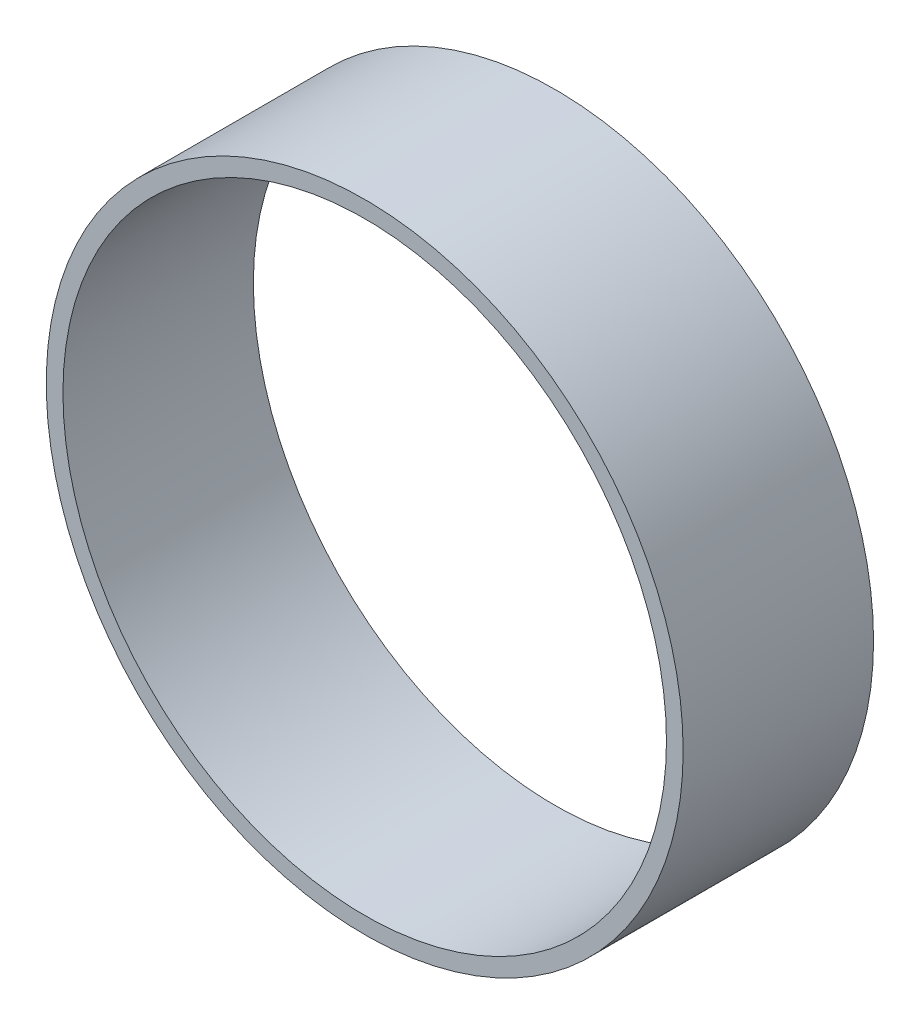
SolidWorks part; units mm, degrees
ref_plane "Front Plane" through (0, 0, 0) normal (0, 0, 1) x (1, 0, 0)
ref_plane "Top Plane" through (0, 0, 0) normal (0, 1, 0) x (1, 0, 0)
ref_plane "Right Plane" through (0, 0, 0) normal (1, 0, 0) x (0, 0, -1)
sketch "Sketch2" plane through (0, 0, 0) normal (0, 1, 0) x (1, 0, 0)
  line L0 (0, 0) -> (-48.5, 0)
  line L1 (-48.5, 0) -> (-48.5, 29)
  line L2 (-48.5, 29) -> (0, 29)
  line L3 (0, 0) -> (0, 74.6303) construction
  line L4 (-45.96, 29) -> (-45.96, 0)
  dimension "D1" = 29
  dimension "D2" = 48.5
  dimension "D3" = 2.54
revolve "Revolve1" add sketch "Sketch2" angle 360 about L3
